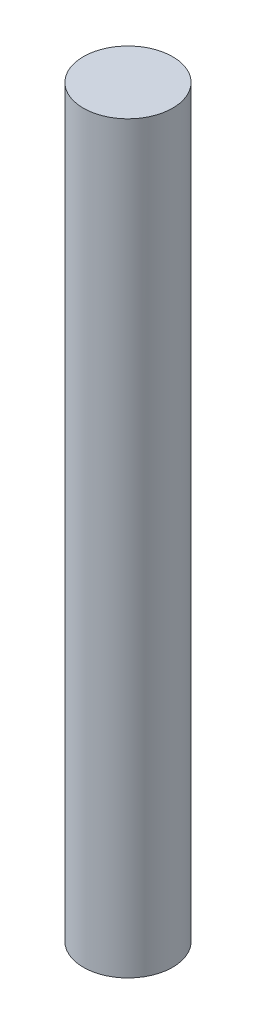
SolidWorks part; units mm, degrees
material "AISI 316 Stainless Steel Sheet (SS)"
ref_plane "Front Plane" through (0, 0, 0) normal (0, 0, 1) x (1, 0, 0)
ref_plane "Top Plane" through (0, 0, 0) normal (0, 1, 0) x (1, 0, 0)
ref_plane "Right Plane" through (0, 0, 0) normal (1, 0, 0) x (0, 0, -1)
sketch "Sketch1" plane through (0, 0, 0) normal (0, 1, 0) x (1, 0, 0)
  circle A0 centre (0, 0) radius 3
extrude "Boss-Extrude1" add sketch "Sketch1" along normal blind 50
sketch "Sketch2" plane through (0, 0, 0) normal (0, -1, 0) x (1, 0, 0)
  line L0 (-2.2361, -2) -> (2.2361, -2)
  arc A0 (-2.2361, -2) -> (2.2361, -2) centre (0, 0) ccw
  dimension "D1" = 6
  dimension "D2" = 2
extrude "Cut-Extrude1" cut sketch "Sketch2" against normal blind 5
